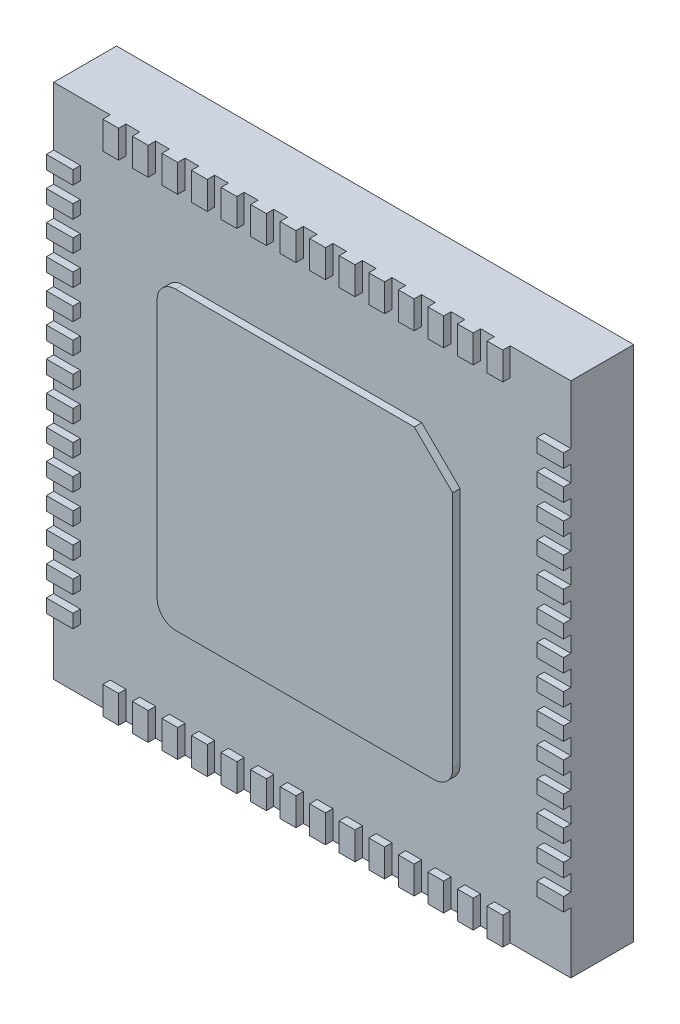
SolidWorks part; units mm, degrees
material "Plastique personnalisé"
ref_plane "Plan de face" through (0, 0, 0) normal (0, 0, 1) x (1, 0, 0)
ref_plane "Plan de dessus" through (0, 0, 0) normal (0, 1, 0) x (1, 0, 0)
ref_plane "Plan de droite" through (0, 0, 0) normal (1, 0, 0) x (0, 0, -1)
sketch "package" plane through (0, 0, 0) normal (0, 0, 1) x (1, 0, 0)
  line L0 (23.2812, 236.9529) -> (30.2812, 236.9529) construction
  line L1 (23.3092, 236.9405) -> (30.3092, 229.9405) construction
  line L2 (23.3092, 236.9405) -> (30.3092, 236.9405)
  line L3 (23.3092, 236.9405) -> (23.3092, 229.9405)
  line L4 (23.3092, 229.9405) -> (30.3092, 229.9405)
  line L5 (30.3092, 236.9405) -> (30.3092, 229.9405)
  dimension "D1" = 7
  dimension "D2" = 7
  dimension "D3" = 7
sketch "Esquisse2" plane through (0, 0, 0) normal (0, 0, 1) x (1, 0, 0)
  line L0 (23.3092, 236.9405) -> (30.3092, 229.9405) construction
  line L1 (25.0592, 231.4405) -> (28.5592, 231.4405)
  line L2 (24.8092, 231.6905) -> (24.8092, 235.1905)
  line L3 (25.0592, 235.4405) -> (28.2902, 235.4405)
  line L4 (28.8092, 231.6905) -> (28.8092, 234.928)
  line L5 (24.8092, 231.4405) -> (28.5514, 235.1826) construction
  line L6 (24.8092, 235.4405) -> (28.8092, 231.4405) construction
  line L7 (28.2902, 235.4405) -> (28.8092, 234.928)
  line L8 (23.3092, 236.9405) -> (30.3092, 236.9405) construction
  line L9 (24.0739, 236.9405) -> (24.2874, 236.9405)
  line L10 (24.0739, 236.9405) -> (24.0739, 236.5655)
  line L11 (24.0739, 236.5655) -> (24.2874, 236.5655)
  line L12 (24.2874, 236.9405) -> (24.2874, 236.5655)
  line L13 (24.4739, 236.9405) -> (24.4739, 236.5655)
  line L14 (24.4739, 236.9405) -> (24.6874, 236.9405)
  line L15 (24.6874, 236.9405) -> (24.6874, 236.5655)
  line L16 (24.4739, 236.5655) -> (24.6874, 236.5655)
  line L17 (24.8739, 236.9405) -> (24.8739, 236.5655)
  line L18 (24.8739, 236.9405) -> (25.0874, 236.9405)
  line L19 (25.0874, 236.9405) -> (25.0874, 236.5655)
  line L20 (24.8739, 236.5655) -> (25.0874, 236.5655)
  line L21 (25.2739, 236.9405) -> (25.2739, 236.5655)
  line L22 (25.2739, 236.9405) -> (25.4874, 236.9405)
  line L23 (25.4874, 236.9405) -> (25.4874, 236.5655)
  line L24 (25.2739, 236.5655) -> (25.4874, 236.5655)
  line L25 (25.6739, 236.9405) -> (25.6739, 236.5655)
  line L26 (25.6739, 236.9405) -> (25.8874, 236.9405)
  line L27 (25.8874, 236.9405) -> (25.8874, 236.5655)
  line L28 (25.6739, 236.5655) -> (25.8874, 236.5655)
  line L29 (26.0739, 236.9405) -> (26.0739, 236.5655)
  line L30 (26.0739, 236.9405) -> (26.2874, 236.9405)
  line L31 (26.2874, 236.9405) -> (26.2874, 236.5655)
  line L32 (26.0739, 236.5655) -> (26.2874, 236.5655)
  line L33 (26.4739, 236.9405) -> (26.4739, 236.5655)
  line L34 (26.4739, 236.9405) -> (26.6874, 236.9405)
  line L35 (26.6874, 236.9405) -> (26.6874, 236.5655)
  line L36 (26.4739, 236.5655) -> (26.6874, 236.5655)
  line L37 (26.8739, 236.9405) -> (26.8739, 236.5655)
  line L38 (26.8739, 236.9405) -> (27.0874, 236.9405)
  line L39 (27.0874, 236.9405) -> (27.0874, 236.5655)
  line L40 (26.8739, 236.5655) -> (27.0874, 236.5655)
  line L41 (27.2739, 236.9405) -> (27.2739, 236.5655)
  line L42 (27.2739, 236.9405) -> (27.4874, 236.9405)
  line L43 (27.4874, 236.9405) -> (27.4874, 236.5655)
  line L44 (27.2739, 236.5655) -> (27.4874, 236.5655)
  line L45 (27.6739, 236.9405) -> (27.6739, 236.5655)
  line L46 (27.6739, 236.9405) -> (27.8874, 236.9405)
  line L47 (27.8874, 236.9405) -> (27.8874, 236.5655)
  line L48 (27.6739, 236.5655) -> (27.8874, 236.5655)
  line L49 (28.0739, 236.9405) -> (28.0739, 236.5655)
  line L50 (28.0739, 236.9405) -> (28.2874, 236.9405)
  line L51 (28.2874, 236.9405) -> (28.2874, 236.5655)
  line L52 (28.0739, 236.5655) -> (28.2874, 236.5655)
  line L53 (28.4739, 236.9405) -> (28.4739, 236.5655)
  line L54 (28.4739, 236.9405) -> (28.6874, 236.9405)
  line L55 (28.6874, 236.9405) -> (28.6874, 236.5655)
  line L56 (28.4739, 236.5655) -> (28.6874, 236.5655)
  line L57 (28.8739, 236.9405) -> (28.8739, 236.5655)
  line L58 (28.8739, 236.9405) -> (29.0874, 236.9405)
  line L59 (29.0874, 236.9405) -> (29.0874, 236.5655)
  line L60 (28.8739, 236.5655) -> (29.0874, 236.5655)
  line L61 (29.2739, 236.9405) -> (29.2739, 236.5655)
  line L62 (29.2739, 236.9405) -> (29.4874, 236.9405)
  line L63 (29.4874, 236.9405) -> (29.4874, 236.5655)
  line L64 (29.2739, 236.5655) -> (29.4874, 236.5655)
  line L65 (23.3092, 233.4405) -> (30.3092, 233.4405) construction
  line L66 (23.3092, 236.9405) -> (23.3092, 229.9405) construction
  line L67 (30.3092, 236.9405) -> (30.3092, 229.9405) construction
  line L68 (23.3092, 235.7459) -> (23.3092, 235.5634)
  line L69 (23.3092, 236.1459) -> (23.6693, 236.1459)
  line L70 (23.3092, 236.1459) -> (23.3092, 235.9634)
  line L71 (23.3092, 235.9634) -> (23.6693, 235.9634)
  line L72 (23.6693, 236.1459) -> (23.6693, 235.9634)
  line L73 (23.3092, 235.7459) -> (23.6693, 235.7459)
  line L74 (23.6693, 235.7459) -> (23.6693, 235.5634)
  line L75 (23.3092, 235.5634) -> (23.6693, 235.5634)
  line L76 (23.3092, 235.3459) -> (23.3092, 235.1634)
  line L77 (23.3092, 235.3459) -> (23.6693, 235.3459)
  line L78 (23.6693, 235.3459) -> (23.6693, 235.1634)
  line L79 (23.3092, 235.1634) -> (23.6693, 235.1634)
  line L80 (23.3092, 234.9459) -> (23.3092, 234.7634)
  line L81 (23.3092, 234.9459) -> (23.6693, 234.9459)
  line L82 (23.6693, 234.9459) -> (23.6693, 234.7634)
  line L83 (23.3092, 234.7634) -> (23.6693, 234.7634)
  line L84 (23.3092, 234.5459) -> (23.3092, 234.3634)
  line L85 (23.3092, 234.5459) -> (23.6693, 234.5459)
  line L86 (23.6693, 234.5459) -> (23.6693, 234.3634)
  line L87 (23.3092, 234.3634) -> (23.6693, 234.3634)
  line L88 (23.3092, 234.1459) -> (23.3092, 233.9634)
  line L89 (23.3092, 234.1459) -> (23.6693, 234.1459)
  line L90 (23.6693, 234.1459) -> (23.6693, 233.9634)
  line L91 (23.3092, 233.9634) -> (23.6693, 233.9634)
  line L92 (23.3092, 233.7459) -> (23.3092, 233.5634)
  line L93 (23.3092, 233.7459) -> (23.6693, 233.7459)
  line L94 (23.6693, 233.7459) -> (23.6693, 233.5634)
  line L95 (23.3092, 233.5634) -> (23.6693, 233.5634)
  line L96 (23.3092, 233.3459) -> (23.3092, 233.1634)
  line L97 (23.3092, 233.3459) -> (23.6693, 233.3459)
  line L98 (23.6693, 233.3459) -> (23.6693, 233.1634)
  line L99 (23.3092, 233.1634) -> (23.6693, 233.1634)
  line L100 (23.3092, 232.9459) -> (23.3092, 232.7634)
  line L101 (23.3092, 232.9459) -> (23.6693, 232.9459)
  line L102 (23.6693, 232.9459) -> (23.6693, 232.7634)
  line L103 (23.3092, 232.7634) -> (23.6693, 232.7634)
  line L104 (23.3092, 232.5459) -> (23.3092, 232.3634)
  line L105 (23.3092, 232.5459) -> (23.6693, 232.5459)
  line L106 (23.6693, 232.5459) -> (23.6693, 232.3634)
  line L107 (23.3092, 232.3634) -> (23.6693, 232.3634)
  line L108 (23.3092, 232.1459) -> (23.3092, 231.9634)
  line L109 (23.3092, 232.1459) -> (23.6693, 232.1459)
  line L110 (23.6693, 232.1459) -> (23.6693, 231.9634)
  line L111 (23.3092, 231.9634) -> (23.6693, 231.9634)
  line L112 (23.3092, 231.7459) -> (23.3092, 231.5634)
  line L113 (23.3092, 231.7459) -> (23.6693, 231.7459)
  line L114 (23.6693, 231.7459) -> (23.6693, 231.5634)
  line L115 (23.3092, 231.5634) -> (23.6693, 231.5634)
  line L116 (23.3092, 231.3459) -> (23.3092, 231.1634)
  line L117 (23.3092, 231.3459) -> (23.6693, 231.3459)
  line L118 (23.6693, 231.3459) -> (23.6693, 231.1634)
  line L119 (23.3092, 231.1634) -> (23.6693, 231.1634)
  line L120 (23.3092, 230.9459) -> (23.3092, 230.7634)
  line L121 (23.3092, 230.9459) -> (23.6693, 230.9459)
  line L122 (23.6693, 230.9459) -> (23.6693, 230.7634)
  line L123 (23.3092, 230.7634) -> (23.6693, 230.7634)
  line L124 (29.2739, 229.9405) -> (29.4874, 229.9405)
  line L125 (29.2739, 229.9405) -> (29.2739, 230.3154)
  line L126 (29.2739, 230.3154) -> (29.4874, 230.3154)
  line L127 (29.4874, 229.9405) -> (29.4874, 230.3154)
  line L128 (28.8739, 229.9405) -> (29.0874, 229.9405)
  line L129 (28.8739, 229.9405) -> (28.8739, 230.3154)
  line L130 (28.8739, 230.3154) -> (29.0874, 230.3154)
  line L131 (29.0874, 229.9405) -> (29.0874, 230.3154)
  line L132 (28.4739, 229.9405) -> (28.6874, 229.9405)
  line L133 (28.4739, 229.9405) -> (28.4739, 230.3154)
  line L134 (28.4739, 230.3154) -> (28.6874, 230.3154)
  line L135 (28.6874, 229.9405) -> (28.6874, 230.3154)
  line L136 (28.0739, 229.9405) -> (28.2874, 229.9405)
  line L137 (28.0739, 229.9405) -> (28.0739, 230.3154)
  line L138 (28.0739, 230.3154) -> (28.2874, 230.3154)
  line L139 (28.2874, 229.9405) -> (28.2874, 230.3154)
  line L140 (27.6739, 229.9405) -> (27.8874, 229.9405)
  line L141 (27.6739, 229.9405) -> (27.6739, 230.3154)
  line L142 (27.6739, 230.3154) -> (27.8874, 230.3154)
  line L143 (27.8874, 229.9405) -> (27.8874, 230.3154)
  line L144 (27.2739, 229.9405) -> (27.4874, 229.9405)
  line L145 (27.2739, 229.9405) -> (27.2739, 230.3154)
  line L146 (27.2739, 230.3154) -> (27.4874, 230.3154)
  line L147 (27.4874, 229.9405) -> (27.4874, 230.3154)
  line L148 (26.8739, 229.9405) -> (27.0874, 229.9405)
  line L149 (26.8739, 229.9405) -> (26.8739, 230.3154)
  line L150 (26.8739, 230.3154) -> (27.0874, 230.3154)
  line L151 (27.0874, 229.9405) -> (27.0874, 230.3154)
  line L152 (26.4739, 229.9405) -> (26.6874, 229.9405)
  line L153 (26.4739, 229.9405) -> (26.4739, 230.3154)
  line L154 (26.4739, 230.3154) -> (26.6874, 230.3154)
  line L155 (26.6874, 229.9405) -> (26.6874, 230.3154)
  line L156 (26.0739, 229.9405) -> (26.2874, 229.9405)
  line L157 (26.0739, 229.9405) -> (26.0739, 230.3154)
  line L158 (26.0739, 230.3154) -> (26.2874, 230.3154)
  line L159 (26.2874, 229.9405) -> (26.2874, 230.3154)
  line L160 (25.6739, 229.9405) -> (25.8874, 229.9405)
  line L161 (25.6739, 229.9405) -> (25.6739, 230.3154)
  line L162 (25.6739, 230.3154) -> (25.8874, 230.3154)
  line L163 (25.8874, 229.9405) -> (25.8874, 230.3154)
  line L164 (25.2739, 229.9405) -> (25.4874, 229.9405)
  line L165 (25.2739, 229.9405) -> (25.2739, 230.3154)
  line L166 (25.2739, 230.3154) -> (25.4874, 230.3154)
  line L167 (25.4874, 229.9405) -> (25.4874, 230.3154)
  line L168 (24.8739, 229.9405) -> (25.0874, 229.9405)
  line L169 (24.8739, 229.9405) -> (24.8739, 230.3154)
  line L170 (24.8739, 230.3154) -> (25.0874, 230.3154)
  line L171 (25.0874, 229.9405) -> (25.0874, 230.3154)
  line L172 (24.4739, 229.9405) -> (24.4739, 230.3154)
  line L173 (24.4739, 229.9405) -> (24.6874, 229.9405)
  line L174 (24.6874, 229.9405) -> (24.6874, 230.3154)
  line L175 (24.4739, 230.3154) -> (24.6874, 230.3154)
  line L176 (24.0739, 229.9405) -> (24.2874, 229.9405)
  line L177 (24.0739, 229.9405) -> (24.0739, 230.3154)
  line L178 (24.0739, 230.3154) -> (24.2874, 230.3154)
  line L179 (24.2874, 229.9405) -> (24.2874, 230.3154)
  line L180 (26.8092, 233.4405) -> (26.8092, 227.4047) construction
  line L181 (30.3092, 230.7634) -> (29.9491, 230.7634)
  line L182 (29.9491, 230.9459) -> (29.9491, 230.7634)
  line L183 (30.3092, 230.9459) -> (29.9491, 230.9459)
  line L184 (30.3092, 230.9459) -> (30.3092, 230.7634)
  line L185 (30.3092, 231.1634) -> (29.9491, 231.1634)
  line L186 (29.9491, 231.3459) -> (29.9491, 231.1634)
  line L187 (30.3092, 231.3459) -> (29.9491, 231.3459)
  line L188 (30.3092, 231.3459) -> (30.3092, 231.1634)
  line L189 (30.3092, 231.5634) -> (29.9491, 231.5634)
  line L190 (29.9491, 231.7459) -> (29.9491, 231.5634)
  line L191 (30.3092, 231.7459) -> (29.9491, 231.7459)
  line L192 (30.3092, 231.7459) -> (30.3092, 231.5634)
  line L193 (30.3092, 231.9634) -> (29.9491, 231.9634)
  line L194 (29.9491, 232.1459) -> (29.9491, 231.9634)
  line L195 (30.3092, 232.1459) -> (29.9491, 232.1459)
  line L196 (30.3092, 232.1459) -> (30.3092, 231.9634)
  line L197 (30.3092, 232.3634) -> (29.9491, 232.3634)
  line L198 (29.9491, 232.5459) -> (29.9491, 232.3634)
  line L199 (30.3092, 232.5459) -> (29.9491, 232.5459)
  line L200 (30.3092, 232.5459) -> (30.3092, 232.3634)
  line L201 (30.3092, 232.7634) -> (29.9491, 232.7634)
  line L202 (29.9491, 232.9459) -> (29.9491, 232.7634)
  line L203 (30.3092, 232.9459) -> (29.9491, 232.9459)
  line L204 (30.3092, 232.9459) -> (30.3092, 232.7634)
  line L205 (30.3092, 233.1634) -> (29.9491, 233.1634)
  line L206 (29.9491, 233.3459) -> (29.9491, 233.1634)
  line L207 (30.3092, 233.3459) -> (29.9491, 233.3459)
  line L208 (30.3092, 233.3459) -> (30.3092, 233.1634)
  line L209 (30.3092, 233.5634) -> (29.9491, 233.5634)
  line L210 (29.9491, 233.7459) -> (29.9491, 233.5634)
  line L211 (30.3092, 233.7459) -> (29.9491, 233.7459)
  line L212 (30.3092, 233.7459) -> (30.3092, 233.5634)
  line L213 (30.3092, 233.9634) -> (29.9491, 233.9634)
  line L214 (29.9491, 234.1459) -> (29.9491, 233.9634)
  line L215 (30.3092, 234.1459) -> (29.9491, 234.1459)
  line L216 (30.3092, 234.1459) -> (30.3092, 233.9634)
  line L217 (30.3092, 234.3634) -> (29.9491, 234.3634)
  line L218 (29.9491, 234.5459) -> (29.9491, 234.3634)
  line L219 (30.3092, 234.5459) -> (29.9491, 234.5459)
  line L220 (30.3092, 234.5459) -> (30.3092, 234.3634)
  line L221 (30.3092, 234.7634) -> (29.9491, 234.7634)
  line L222 (29.9491, 234.9459) -> (29.9491, 234.7634)
  line L223 (30.3092, 234.9459) -> (29.9491, 234.9459)
  line L224 (30.3092, 234.9459) -> (30.3092, 234.7634)
  line L225 (30.3092, 235.1634) -> (29.9491, 235.1634)
  line L226 (29.9491, 235.3459) -> (29.9491, 235.1634)
  line L227 (30.3092, 235.3459) -> (29.9491, 235.3459)
  line L228 (30.3092, 235.3459) -> (30.3092, 235.1634)
  line L229 (30.3092, 235.5634) -> (29.9491, 235.5634)
  line L230 (29.9491, 235.7459) -> (29.9491, 235.5634)
  line L231 (30.3092, 235.7459) -> (29.9491, 235.7459)
  line L232 (29.9491, 236.1459) -> (29.9491, 235.9634)
  line L233 (30.3092, 235.9634) -> (29.9491, 235.9634)
  line L234 (30.3092, 236.1459) -> (30.3092, 235.9634)
  line L235 (30.3092, 236.1459) -> (29.9491, 236.1459)
  line L236 (30.3092, 235.7459) -> (30.3092, 235.5634)
  arc A0 (28.5592, 231.4405) -> (28.8092, 231.6905) centre (28.5592, 231.6905) ccw
  arc A1 (25.0592, 231.4405) -> (24.8092, 231.6905) centre (25.0592, 231.6905) cw
  arc A2 (24.8092, 235.1905) -> (25.0592, 235.4405) centre (25.0592, 235.1905) cw
  point P0 (26.8092, 233.4405)
  dimension "D1" = 0.25
  dimension "D2" = 4
  dimension "D3" = 14
  dimension "D4" = 14
extrude "Boss.-Extru.1" add sketch "package" against normal blind 0.85
extrude "Boss.-Extru.2" add sketch "Esquisse2" along normal blind 0.1
sketch "Esquisse3" plane through (0, 0, -0.85) normal (0, 0, -1) x (-1, 0, 0)
  circle A0 centre (-29.9746, 236.5813) radius 0.1661
extrude "Enlèv. mat.-Extru.1" cut sketch "Esquisse3" against normal blind 0.1
sketch "Esquisse4" plane through (-0.3704, 1.1024, -0.85) normal (0, 0, -1) x (-1, 0, 0)
  line L8 (-28.6829, 230.452) -> (-28.6867, 230.4847)
  line L9 (-28.6867, 230.4847) -> (-28.8383, 230.4808)
  line L10 (-28.8383, 230.4808) -> (-28.99, 230.4769)
  line L11 (-28.99, 230.4769) -> (-28.99, 230.5964)
  line L12 (-28.99, 230.5964) -> (-28.99, 230.7159)
  line L13 (-28.99, 230.7159) -> (-28.8562, 230.7193)
  line L14 (-28.8562, 230.7193) -> (-28.7223, 230.7226)
  line L15 (-28.7223, 230.7226) -> (-28.7223, 230.7524)
  line L16 (-28.7223, 230.7524) -> (-28.7223, 230.7821)
  line L17 (-28.7223, 230.7821) -> (-28.8562, 230.7855)
  line L18 (-28.8562, 230.7855) -> (-28.99, 230.7888)
  line L19 (-28.99, 230.7888) -> (-28.99, 230.9015)
  line L20 (-28.99, 230.9015) -> (-28.99, 231.0141)
  line L21 (-28.99, 231.0141) -> (-28.8413, 231.0141)
  line L22 (-28.8413, 231.0141) -> (-28.6926, 231.0141)
  line L23 (-28.6926, 231.0141) -> (-28.6926, 231.0438)
  line L24 (-28.6926, 231.0438) -> (-28.6926, 231.0736)
  line L25 (-28.6926, 231.0736) -> (-28.877, 231.0736)
  line L26 (-28.877, 231.0736) -> (-29.0614, 231.0736)
  line L27 (-29.0614, 231.0736) -> (-29.0614, 230.7464)
  line L28 (-29.0614, 230.7464) -> (-29.0614, 230.4193)
  line L29 (-29.0614, 230.4193) -> (-28.8703, 230.4193)
  line L30 (-28.8703, 230.4193) -> (-28.6791, 230.4193)
  line L31 (-28.6791, 230.4193) -> (-28.6829, 230.452)
  line L32 (-28.0383, 230.5561) -> (-28.0383, 230.6929)
  line L33 (-28.0383, 230.6929) -> (-27.936, 230.6929)
  line L34 (-27.9661, 231.0708) -> (-28.102, 231.0676)
  line L35 (-28.102, 231.0676) -> (-28.0999, 230.7464)
  line L36 (-28.0681, 230.4193) -> (-28.0383, 230.4193)
  line L37 (-28.0383, 230.4193) -> (-28.0383, 230.5561)
  line L38 (-28.0383, 230.8832) -> (-28.0383, 231.0141)
  line L39 (-28.0383, 231.0141) -> (-27.9485, 231.0141)
  line L40 (-27.9485, 230.7524) -> (-28.0383, 230.7524)
  line L41 (-28.0383, 230.7524) -> (-28.0383, 230.8832)
  line L42 (-26.8488, 230.4526) -> (-26.8488, 230.4858)
  line L43 (-26.8488, 230.4858) -> (-26.9614, 230.4809)
  line L44 (-27.0213, 230.4193) -> (-26.8488, 230.4193)
  line L45 (-26.8488, 230.4193) -> (-26.8488, 230.4526)
  line L46 (-26.3989, 230.7459) -> (-26.3951, 230.7762)
  line L47 (-26.3951, 230.7762) -> (-26.5803, 230.7762)
  line L48 (-26.5803, 230.7762) -> (-26.7655, 230.7762)
  line L49 (-26.7655, 230.7762) -> (-26.7655, 230.7484)
  line L50 (-26.5791, 230.7132) -> (-26.4027, 230.7156)
  line L51 (-26.4027, 230.7156) -> (-26.3989, 230.7459)
  line L52 (-26.2439, 232.1836) -> (-26.2161, 232.2135)
  line L53 (-26.2161, 232.2135) -> (-26.2512, 232.2502)
  line L54 (-28.1351, 234.1342) -> (-28.1724, 234.1715)
  line L55 (-28.1724, 234.1715) -> (-28.2316, 234.1066)
  line L56 (-26.9889, 232.0679) -> (-26.8971, 232.0359)
  line L57 (-26.8971, 232.0359) -> (-26.8013, 232.069)
  line L58 (-26.2003, 232.5814) -> (-26.1572, 232.6439)
  line L59 (-26.1572, 232.6439) -> (-26.1821, 232.7689)
  line L60 (-27.6008, 234.2028) -> (-27.7112, 234.2254)
  line L61 (-27.7112, 234.2254) -> (-27.804, 234.1694)
  line L62 (-27.9383, 234.0792) -> (-27.9798, 234.045)
  line L63 (-27.9798, 234.045) -> (-27.9764, 233.9541)
  line L64 (-27.9764, 233.9541) -> (-27.9729, 233.8631)
  line L65 (-27.9729, 233.8631) -> (-27.9313, 233.8602)
  line L66 (-26.5276, 232.4654) -> (-26.5276, 232.4059)
  line L67 (-26.5276, 232.4059) -> (-26.4235, 232.4061)
  line L68 (-26.4235, 232.4061) -> (-26.3194, 232.4063)
  line L69 (-26.3194, 232.4063) -> (-26.2814, 232.4626)
  line L70 (-27.1822, 234.3566) -> (-27.2956, 234.3568)
  line L71 (-27.2956, 234.3568) -> (-27.3097, 234.3194)
  spline S0 degree 3 poles (-28.3034, 230.4273) (-28.2435, 230.4557) (-28.2169, 230.5058) (-28.2168, 230.5902) knots 0 0 0 0 1 1 1 1
  spline S1 degree 3 poles (-28.2168, 230.5902) (-28.2168, 230.6551) (-28.2199, 230.6631) (-28.2614, 230.7044) knots 0 0 0 0 1 1 1 1
  spline S2 degree 3 poles (-28.2614, 230.7044) (-28.2883, 230.7311) (-28.3343, 230.7589) (-28.3774, 230.7744) knots 0 0 0 0 1 1 1 1
  spline S3 degree 3 poles (-28.3774, 230.7744) (-28.4701, 230.8078) (-28.5031, 230.8271) (-28.531, 230.864) knots 0 0 0 0 1 1 1 1
  spline S4 degree 3 poles (-28.531, 230.864) (-28.5509, 230.8904) (-28.5521, 230.9002) (-28.5401, 230.9402) knots 0 0 0 0 1 1 1 1
  spline S5 degree 3 poles (-28.5401, 230.9402) (-28.5132, 231.03) (-28.3832, 231.0483) (-28.312, 230.9725) knots 0 0 0 0 1 1 1 1
  spline S6 degree 3 poles (-28.312, 230.9725) (-28.2821, 230.9407) (-28.2681, 230.9369) (-28.2419, 230.9536) knots 0 0 0 0 1 1 1 1
  spline S7 degree 3 poles (-28.2419, 230.9536) (-28.2165, 230.9696) (-28.269, 231.0357) (-28.3286, 231.0628) knots 0 0 0 0 1 1 1 1
  spline S8 degree 3 poles (-28.3286, 231.0628) (-28.4159, 231.1024) (-28.5158, 231.084) (-28.5742, 231.0176) knots 0 0 0 0 1 1 1 1
  spline S9 degree 3 poles (-28.5742, 231.0176) (-28.6039, 230.9838) (-28.6093, 230.9675) (-28.6093, 230.913) knots 0 0 0 0 1 1 1 1
  spline S10 degree 3 poles (-28.6093, 230.913) (-28.6093, 230.8584) (-28.6039, 230.8422) (-28.5742, 230.8084) knots 0 0 0 0 1 1 1 1
  spline S11 degree 3 poles (-28.5742, 230.8084) (-28.5549, 230.7864) (-28.5161, 230.7586) (-28.488, 230.7467) knots 0 0 0 0 1 1 1 1
  spline S12 degree 3 poles (-28.488, 230.7467) (-28.3184, 230.6746) (-28.3112, 230.6703) (-28.2948, 230.6309) knots 0 0 0 0 1 1 1 1
  spline S13 degree 3 poles (-28.2948, 230.6309) (-28.2726, 230.5779) (-28.2837, 230.5322) (-28.3277, 230.4952) knots 0 0 0 0 1 1 1 1
  spline S14 degree 3 poles (-28.3277, 230.4952) (-28.3598, 230.4682) (-28.3724, 230.465) (-28.4293, 230.4697) knots 0 0 0 0 1 1 1 1
  spline S15 degree 3 poles (-28.4293, 230.4697) (-28.486, 230.4744) (-28.4995, 230.4808) (-28.5353, 230.5199) knots 0 0 0 0 1 1 1 1
  spline S16 degree 3 poles (-28.5353, 230.5199) (-28.5717, 230.5596) (-28.5795, 230.5632) (-28.6047, 230.5517) knots 0 0 0 0 1 1 1 1
  spline S17 degree 3 poles (-28.6047, 230.5517) (-28.6385, 230.5363) (-28.6393, 230.5287) (-28.6107, 230.4944) knots 0 0 0 0 1 1 1 1
  spline S18 degree 3 poles (-28.6107, 230.4944) (-28.56, 230.4337) (-28.5029, 230.4074) (-28.4221, 230.4074) knots 0 0 0 0 1 1 1 1
  spline S19 degree 3 poles (-28.4221, 230.4074) (-28.375, 230.4074) (-28.3291, 230.4151) (-28.3034, 230.4273) knots 0 0 0 0 1 1 1 1
  spline S20 degree 3 poles (-27.3472, 230.4344) (-27.287, 230.4746) (-27.2629, 230.5298) (-27.2683, 230.6148) knots 0 0 0 0 1 1 1 1
  spline S21 degree 3 poles (-27.2683, 230.6148) (-27.2726, 230.6803) (-27.2765, 230.6885) (-27.3226, 230.7295) knots 0 0 0 0 1 1 1 1
  spline S22 degree 3 poles (-27.3226, 230.7295) (-27.3599, 230.7626) (-27.3679, 230.7753) (-27.3545, 230.7804) knots 0 0 0 0 1 1 1 1
  spline S23 degree 3 poles (-27.3545, 230.7804) (-27.3245, 230.7919) (-27.289, 230.8628) (-27.2889, 230.9112) knots 0 0 0 0 1 1 1 1
  spline S24 degree 3 poles (-27.2889, 230.9112) (-27.2889, 230.9787) (-27.3205, 231.0353) (-27.3733, 231.0623) knots 0 0 0 0 1 1 1 1
  spline S25 degree 3 poles (-27.3733, 231.0623) (-27.4562, 231.1045) (-27.5337, 231.0859) (-27.5916, 231.01) knots 0 0 0 0 1 1 1 1
  spline S26 degree 3 poles (-27.5916, 231.01) (-27.6281, 230.9622) (-27.6294, 230.9475) (-27.5986, 230.931) knots 0 0 0 0 1 1 1 1
  spline S27 degree 3 poles (-27.5986, 230.931) (-27.5787, 230.9204) (-27.5724, 230.924) (-27.5562, 230.9553) knots 0 0 0 0 1 1 1 1
  spline S28 degree 3 poles (-27.5562, 230.9553) (-27.5016, 231.0608) (-27.3603, 231.0245) (-27.3603, 230.9049) knots 0 0 0 0 1 1 1 1
  spline S29 degree 3 poles (-27.3603, 230.9049) (-27.3603, 230.8453) (-27.3999, 230.8034) (-27.4665, 230.7928) knots 0 0 0 0 1 1 1 1
  spline S30 degree 3 poles (-27.4665, 230.7928) (-27.5073, 230.7862) (-27.5149, 230.7806) (-27.5149, 230.7568) knots 0 0 0 0 1 1 1 1
  spline S31 degree 3 poles (-27.5149, 230.7568) (-27.5149, 230.7324) (-27.5092, 230.7286) (-27.4725, 230.7286) knots 0 0 0 0 1 1 1 1
  spline S32 degree 3 poles (-27.4725, 230.7286) (-27.3876, 230.7286) (-27.3371, 230.6799) (-27.3368, 230.5977) knots 0 0 0 0 1 1 1 1
  spline S33 degree 3 poles (-27.3368, 230.5977) (-27.3365, 230.5246) (-27.3729, 230.4796) (-27.4394, 230.4707) knots 0 0 0 0 1 1 1 1
  spline S34 degree 3 poles (-27.4394, 230.4707) (-27.4943, 230.4633) (-27.5574, 230.4916) (-27.5693, 230.5289) knots 0 0 0 0 1 1 1 1
  spline S35 degree 3 poles (-27.5693, 230.5289) (-27.5763, 230.551) (-27.6054, 230.5565) (-27.6305, 230.5406) knots 0 0 0 0 1 1 1 1
  spline S36 degree 3 poles (-27.6305, 230.5406) (-27.6514, 230.5273) (-27.6085, 230.4609) (-27.5596, 230.4311) knots 0 0 0 0 1 1 1 1
  spline S37 degree 3 poles (-27.5596, 230.4311) (-27.5038, 230.3971) (-27.4006, 230.3987) (-27.3472, 230.4344) knots 0 0 0 0 1 1 1 1
  spline S38 degree 3 poles (-26.004, 230.4291) (-25.9575, 230.4534) (-25.909, 230.535) (-25.909, 230.5888) knots 0 0 0 0 1 1 1 1
  spline S39 degree 3 poles (-25.909, 230.5888) (-25.909, 230.6761) (-25.9685, 230.7335) (-26.1164, 230.7888) knots 0 0 0 0 1 1 1 1
  spline S40 degree 3 poles (-26.1164, 230.7888) (-26.2093, 230.8236) (-26.2421, 230.8568) (-26.2421, 230.9165) knots 0 0 0 0 1 1 1 1
  spline S41 degree 3 poles (-26.2421, 230.9165) (-26.2421, 231.0215) (-26.102, 231.0588) (-26.0176, 230.9763) knots 0 0 0 0 1 1 1 1
  spline S42 degree 3 poles (-26.0176, 230.9763) (-25.9915, 230.9508) (-25.9745, 230.943) (-25.957, 230.9485) knots 0 0 0 0 1 1 1 1
  spline S43 degree 3 poles (-25.957, 230.9485) (-25.9255, 230.9585) (-25.9264, 230.969) (-25.9629, 231.0123) knots 0 0 0 0 1 1 1 1
  spline S44 degree 3 poles (-25.9629, 231.0123) (-26.0454, 231.1104) (-26.2174, 231.1051) (-26.2873, 231.0022) knots 0 0 0 0 1 1 1 1
  spline S45 degree 3 poles (-26.2873, 231.0022) (-26.3106, 230.9679) (-26.3147, 230.9494) (-26.3105, 230.8978) knots 0 0 0 0 1 1 1 1
  spline S46 degree 3 poles (-26.3105, 230.8978) (-26.3038, 230.8139) (-26.2669, 230.7766) (-26.1424, 230.7279) knots 0 0 0 0 1 1 1 1
  spline S47 degree 3 poles (-26.1424, 230.7279) (-26.037, 230.6866) (-25.9804, 230.6387) (-25.9804, 230.591) knots 0 0 0 0 1 1 1 1
  spline S48 degree 3 poles (-25.9804, 230.591) (-25.9804, 230.46) (-26.1641, 230.4208) (-26.2524, 230.533) knots 0 0 0 0 1 1 1 1
  spline S49 degree 3 poles (-26.2524, 230.533) (-26.2701, 230.5555) (-26.2834, 230.5619) (-26.301, 230.5563) knots 0 0 0 0 1 1 1 1
  spline S50 degree 3 poles (-26.301, 230.5563) (-26.3144, 230.552) (-26.3253, 230.5413) (-26.3253, 230.5324) knots 0 0 0 0 1 1 1 1
  spline S51 degree 3 poles (-26.3253, 230.5324) (-26.3253, 230.5069) (-26.2646, 230.4415) (-26.2248, 230.4241) knots 0 0 0 0 1 1 1 1
  spline S52 degree 3 poles (-26.2248, 230.4241) (-26.1707, 230.4006) (-26.0534, 230.4032) (-26.004, 230.4291) knots 0 0 0 0 1 1 1 1
  spline S53 degree 3 poles (-25.5456, 230.4434) (-25.4986, 230.4873) (-25.4807, 230.5302) (-25.4807, 230.5987) knots 0 0 0 0 1 1 1 1
  spline S54 degree 3 poles (-25.4807, 230.5987) (-25.4807, 230.6655) (-25.5117, 230.7308) (-25.5543, 230.7535) knots 0 0 0 0 1 1 1 1
  spline S55 degree 3 poles (-25.5543, 230.7535) (-25.578, 230.7662) (-25.578, 230.7664) (-25.5547, 230.792) knots 0 0 0 0 1 1 1 1
  spline S56 degree 3 poles (-25.5547, 230.792) (-25.5174, 230.8331) (-25.5045, 230.8661) (-25.5046, 230.9211) knots 0 0 0 0 1 1 1 1
  spline S57 degree 3 poles (-25.5046, 230.9211) (-25.5047, 231.0911) (-25.7244, 231.146) (-25.8143, 230.9986) knots 0 0 0 0 1 1 1 1
  spline S58 degree 3 poles (-25.8143, 230.9986) (-25.8433, 230.9511) (-25.8432, 230.9465) (-25.8136, 230.9307) knots 0 0 0 0 1 1 1 1
  spline S59 degree 3 poles (-25.8136, 230.9307) (-25.793, 230.9197) (-25.7867, 230.9229) (-25.7694, 230.953) knots 0 0 0 0 1 1 1 1
  spline S60 degree 3 poles (-25.7694, 230.953) (-25.7281, 231.025) (-25.6602, 231.0386) (-25.6027, 230.9866) knots 0 0 0 0 1 1 1 1
  spline S61 degree 3 poles (-25.6027, 230.9866) (-25.5822, 230.9681) (-25.5759, 230.9493) (-25.5759, 230.907) knots 0 0 0 0 1 1 1 1
  spline S62 degree 3 poles (-25.5759, 230.907) (-25.5759, 230.8367) (-25.6126, 230.7972) (-25.6796, 230.7953) knots 0 0 0 0 1 1 1 1
  spline S63 degree 3 poles (-25.6796, 230.7953) (-25.7195, 230.7941) (-25.725, 230.7903) (-25.7284, 230.7613) knots 0 0 0 0 1 1 1 1
  spline S64 degree 3 poles (-25.7284, 230.7613) (-25.732, 230.7299) (-25.73, 230.7286) (-25.6791, 230.7286) knots 0 0 0 0 1 1 1 1
  spline S65 degree 3 poles (-25.6791, 230.7286) (-25.6369, 230.7286) (-25.6184, 230.7215) (-25.5891, 230.6941) knots 0 0 0 0 1 1 1 1
  spline S66 degree 3 poles (-25.5891, 230.6941) (-25.5569, 230.6641) (-25.5521, 230.6515) (-25.5521, 230.598) knots 0 0 0 0 1 1 1 1
  spline S67 degree 3 poles (-25.5521, 230.598) (-25.5521, 230.5458) (-25.5574, 230.5311) (-25.5869, 230.5016) knots 0 0 0 0 1 1 1 1
  spline S68 degree 3 poles (-25.5869, 230.5016) (-25.6388, 230.4498) (-25.7066, 230.4524) (-25.7627, 230.5085) knots 0 0 0 0 1 1 1 1
  spline S69 degree 3 poles (-25.7627, 230.5085) (-25.8075, 230.5533) (-25.8115, 230.555) (-25.8358, 230.5396) knots 0 0 0 0 1 1 1 1
  spline S70 degree 3 poles (-25.8358, 230.5396) (-25.8591, 230.5249) (-25.8232, 230.4605) (-25.7746, 230.43) knots 0 0 0 0 1 1 1 1
  spline S71 degree 3 poles (-25.7746, 230.43) (-25.7183, 230.3947) (-25.5898, 230.4022) (-25.5456, 230.4434) knots 0 0 0 0 1 1 1 1
  spline S72 degree 3 poles (-27.936, 230.6929) (-27.7657, 230.6929) (-27.6993, 230.7446) (-27.6994, 230.8773) knots 0 0 0 0 1 1 1 1
  spline S73 degree 3 poles (-27.6994, 230.8773) (-27.6995, 230.9634) (-27.7279, 231.019) (-27.7885, 231.0516) knots 0 0 0 0 1 1 1 1
  spline S74 degree 3 poles (-27.7885, 231.0516) (-27.8236, 231.0705) (-27.8516, 231.0735) (-27.9661, 231.0708) knots 0 0 0 0 1 1 1 1
  spline S75 degree 3 poles (-28.0999, 230.7464) (-28.0988, 230.5698) (-28.0979, 230.4239) (-28.0979, 230.4223) knots 0 0 0 0 1 1 1 1
  spline S76 degree 3 poles (-28.0979, 230.4223) (-28.0979, 230.4206) (-28.0844, 230.4193) (-28.0681, 230.4193) knots 0 0 0 0 1 1 1 1
  spline S77 degree 3 poles (-27.9485, 231.0141) (-27.8166, 231.0141) (-27.7647, 230.9771) (-27.7647, 230.8832) knots 0 0 0 0 1 1 1 1
  spline S78 degree 3 poles (-27.7647, 230.8832) (-27.7647, 230.7893) (-27.8166, 230.7524) (-27.9485, 230.7524) knots 0 0 0 0 1 1 1 1
  spline S79 degree 3 poles (-26.9614, 230.4809) (-27.1059, 230.4746) (-27.1174, 230.4785) (-27.0929, 230.5257) knots 0 0 0 0 1 1 1 1
  spline S80 degree 3 poles (-27.0929, 230.5257) (-27.0828, 230.5453) (-27.0348, 230.6037) (-26.9863, 230.6557) knots 0 0 0 0 1 1 1 1
  spline S81 degree 3 poles (-26.9863, 230.6557) (-26.9377, 230.7076) (-26.8869, 230.7718) (-26.8734, 230.7983) knots 0 0 0 0 1 1 1 1
  spline S82 degree 3 poles (-26.8734, 230.7983) (-26.84, 230.8638) (-26.8404, 230.9561) (-26.8744, 231.0111) knots 0 0 0 0 1 1 1 1
  spline S83 degree 3 poles (-26.8744, 231.0111) (-26.9347, 231.1087) (-27.0961, 231.1095) (-27.1549, 231.0125) knots 0 0 0 0 1 1 1 1
  spline S84 degree 3 poles (-27.1549, 231.0125) (-27.1944, 230.9472) (-27.1982, 230.9221) (-27.1709, 230.9075) knots 0 0 0 0 1 1 1 1
  spline S85 degree 3 poles (-27.1709, 230.9075) (-27.1498, 230.8962) (-27.144, 230.9003) (-27.1227, 230.9421) knots 0 0 0 0 1 1 1 1
  spline S86 degree 3 poles (-27.1227, 230.9421) (-27.0951, 230.9962) (-27.0684, 231.0141) (-27.0153, 231.0141) knots 0 0 0 0 1 1 1 1
  spline S87 degree 3 poles (-27.0153, 231.0141) (-26.962, 231.0141) (-26.9359, 230.9963) (-26.9204, 230.9495) knots 0 0 0 0 1 1 1 1
  spline S88 degree 3 poles (-26.9204, 230.9495) (-26.8969, 230.878) (-26.9211, 230.8246) (-27.0354, 230.696) knots 0 0 0 0 1 1 1 1
  spline S89 degree 3 poles (-27.0354, 230.696) (-27.1314, 230.588) (-27.1934, 230.4877) (-27.1936, 230.4401) knots 0 0 0 0 1 1 1 1
  spline S90 degree 3 poles (-27.1936, 230.4401) (-27.1937, 230.4212) (-27.1777, 230.4193) (-27.0213, 230.4193) knots 0 0 0 0 1 1 1 1
  spline S91 degree 3 poles (-26.7655, 230.7484) (-26.7655, 230.7331) (-26.7633, 230.7184) (-26.7605, 230.7157) knots 0 0 0 0 1 1 1 1
  spline S92 degree 3 poles (-26.7605, 230.7157) (-26.7578, 230.713) (-26.6762, 230.7118) (-26.5791, 230.7132) knots 0 0 0 0 1 1 1 1
  spline S93 degree 3 poles (-26.9045, 231.8347) (-26.7387, 231.8711) (-26.6049, 231.9252) (-26.4562, 232.016) knots 0 0 0 0 1 1 1 1
  spline S94 degree 3 poles (-26.4562, 232.016) (-26.401, 232.0497) (-26.2789, 232.1462) (-26.2439, 232.1836) knots 0 0 0 0 1 1 1 1
  spline S95 degree 3 poles (-26.2512, 232.2502) (-26.2705, 232.2704) (-26.2894, 232.2869) (-26.2933, 232.2869) knots 0 0 0 0 1 1 1 1
  spline S96 degree 3 poles (-26.2933, 232.2869) (-26.2972, 232.2869) (-26.3153, 232.2729) (-26.3336, 232.2557) knots 0 0 0 0 1 1 1 1
  spline S97 degree 3 poles (-26.3336, 232.2557) (-26.4695, 232.1282) (-26.6821, 232.0114) (-26.8725, 231.9595) knots 0 0 0 0 1 1 1 1
  spline S98 degree 3 poles (-26.8725, 231.9595) (-27.0127, 231.9213) (-27.2272, 231.9083) (-27.3732, 231.9291) knots 0 0 0 0 1 1 1 1
  spline S99 degree 3 poles (-27.3732, 231.9291) (-27.6004, 231.9616) (-27.8595, 232.0795) (-28.0264, 232.2264) knots 0 0 0 0 1 1 1 1
  spline S100 degree 3 poles (-28.0264, 232.2264) (-28.0676, 232.2625) (-28.0676, 232.2628) (-28.0324, 232.2453) knots 0 0 0 0 1 1 1 1
  spline S101 degree 3 poles (-28.0324, 232.2453) (-27.9349, 232.1969) (-27.8023, 232.2498) (-27.7573, 232.355) knots 0 0 0 0 1 1 1 1
  spline S102 degree 3 poles (-27.7573, 232.355) (-27.736, 232.4047) (-27.7364, 232.4816) (-27.7582, 232.5237) knots 0 0 0 0 1 1 1 1
  spline S103 degree 3 poles (-27.7582, 232.5237) (-27.7827, 232.571) (-27.8516, 232.6282) (-27.8958, 232.6379) knots 0 0 0 0 1 1 1 1
  spline S104 degree 3 poles (-27.8958, 232.6379) (-28.0633, 232.6747) (-28.1968, 232.5184) (-28.1398, 232.3524) knots 0 0 0 0 1 1 1 1
  spline S105 degree 3 poles (-28.1398, 232.3524) (-28.1213, 232.2987) (-28.2531, 232.4739) (-28.3141, 232.5843) knots 0 0 0 0 1 1 1 1
  spline S106 degree 3 poles (-28.3141, 232.5843) (-28.359, 232.6655) (-28.4172, 232.8241) (-28.4375, 232.9205) knots 0 0 0 0 1 1 1 1
  spline S107 degree 3 poles (-28.4375, 232.9205) (-28.5198, 233.311) (-28.4105, 233.7332) (-28.1529, 234.0195) knots 0 0 0 0 1 1 1 1
  spline S108 degree 3 poles (-28.1529, 234.0195) (-28.1226, 234.0532) (-28.0978, 234.0844) (-28.0978, 234.0888) knots 0 0 0 0 1 1 1 1
  spline S109 degree 3 poles (-28.0978, 234.0888) (-28.0978, 234.0933) (-28.1146, 234.1137) (-28.1351, 234.1342) knots 0 0 0 0 1 1 1 1
  spline S110 degree 3 poles (-28.2316, 234.1066) (-28.3948, 233.9273) (-28.5166, 233.6733) (-28.5624, 233.417) knots 0 0 0 0 1 1 1 1
  spline S111 degree 3 poles (-28.5624, 233.417) (-28.5821, 233.3067) (-28.5788, 233.0369) (-28.5564, 232.9293) knots 0 0 0 0 1 1 1 1
  spline S112 degree 3 poles (-28.5564, 232.9293) (-28.4307, 232.3263) (-27.9742, 231.8965) (-27.3686, 231.811) knots 0 0 0 0 1 1 1 1
  spline S113 degree 3 poles (-27.3686, 231.811) (-27.2542, 231.7949) (-27.0354, 231.806) (-26.9045, 231.8347) knots 0 0 0 0 1 1 1 1
  spline S114 degree 3 poles (-27.2678, 232.0698) (-27.2032, 232.1917) (-27.1765, 232.3012) (-27.1771, 232.4416) knots 0 0 0 0 1 1 1 1
  spline S115 degree 3 poles (-27.1771, 232.4416) (-27.1776, 232.5787) (-27.1968, 232.663) (-27.2529, 232.7741) knots 0 0 0 0 1 1 1 1
  spline S116 degree 3 poles (-27.2529, 232.7741) (-27.3794, 233.0247) (-27.5982, 233.1722) (-27.8988, 233.2093) knots 0 0 0 0 1 1 1 1
  spline S117 degree 3 poles (-27.8988, 233.2093) (-27.9901, 233.2206) (-28.0201, 233.2958) (-27.9485, 233.3341) knots 0 0 0 0 1 1 1 1
  spline S118 degree 3 poles (-27.9485, 233.3341) (-27.9236, 233.3474) (-27.9029, 233.3476) (-27.8267, 233.3348) knots 0 0 0 0 1 1 1 1
  spline S119 degree 3 poles (-27.8267, 233.3348) (-27.5105, 233.2821) (-27.2703, 233.109) (-27.14, 232.8401) knots 0 0 0 0 1 1 1 1
  spline S120 degree 3 poles (-27.14, 232.8401) (-27.0599, 232.6747) (-27.0452, 232.6072) (-27.0461, 232.4059) knots 0 0 0 0 1 1 1 1
  spline S121 degree 3 poles (-27.0461, 232.4059) (-27.0467, 232.2544) (-27.05, 232.2263) (-27.0731, 232.1749) knots 0 0 0 0 1 1 1 1
  spline S122 degree 3 poles (-27.0731, 232.1749) (-27.0876, 232.1428) (-27.0952, 232.1127) (-27.0901, 232.1082) knots 0 0 0 0 1 1 1 1
  spline S123 degree 3 poles (-27.0901, 232.1082) (-27.0849, 232.1036) (-27.0394, 232.0855) (-26.9889, 232.0679) knots 0 0 0 0 1 1 1 1
  spline S124 degree 3 poles (-26.8013, 232.069) (-26.7115, 232.1001) (-26.7047, 232.1048) (-26.6943, 232.144) knots 0 0 0 0 1 1 1 1
  spline S125 degree 3 poles (-26.6943, 232.144) (-26.6159, 232.4379) (-26.6774, 232.8278) (-26.8443, 233.0957) knots 0 0 0 0 1 1 1 1
  spline S126 degree 3 poles (-26.8443, 233.0957) (-27.0629, 233.4468) (-27.3616, 233.6458) (-27.7657, 233.7098) knots 0 0 0 0 1 1 1 1
  spline S127 degree 3 poles (-27.7657, 233.7098) (-27.9173, 233.7338) (-28.0097, 233.7251) (-28.1114, 233.6772) knots 0 0 0 0 1 1 1 1
  spline S128 degree 3 poles (-28.1114, 233.6772) (-28.2851, 233.5953) (-28.3666, 233.4529) (-28.3577, 233.2464) knots 0 0 0 0 1 1 1 1
  spline S129 degree 3 poles (-28.3577, 233.2464) (-28.3527, 233.1286) (-28.3164, 233.0452) (-28.2345, 232.9633) knots 0 0 0 0 1 1 1 1
  spline S130 degree 3 poles (-28.2345, 232.9633) (-28.1582, 232.887) (-28.0747, 232.8478) (-27.9603, 232.8346) knots 0 0 0 0 1 1 1 1
  spline S131 degree 3 poles (-27.9603, 232.8346) (-27.8125, 232.8175) (-27.7404, 232.7849) (-27.6498, 232.6943) knots 0 0 0 0 1 1 1 1
  spline S132 degree 3 poles (-27.6498, 232.6943) (-27.5548, 232.5993) (-27.5261, 232.4019) (-27.589, 232.275) knots 0 0 0 0 1 1 1 1
  spline S133 degree 3 poles (-27.589, 232.275) (-27.6068, 232.2391) (-27.6282, 232.2001) (-27.6365, 232.1885) knots 0 0 0 0 1 1 1 1
  spline S134 degree 3 poles (-27.6365, 232.1885) (-27.6499, 232.1698) (-27.6434, 232.1599) (-27.5816, 232.1052) knots 0 0 0 0 1 1 1 1
  spline S135 degree 3 poles (-27.5816, 232.1052) (-27.5198, 232.0505) (-27.5007, 232.0408) (-27.421, 232.0236) knots 0 0 0 0 1 1 1 1
  spline S136 degree 3 poles (-27.421, 232.0236) (-27.3712, 232.0128) (-27.3246, 232.0035) (-27.3173, 232.0027) knots 0 0 0 0 1 1 1 1
  spline S137 degree 3 poles (-27.3173, 232.0027) (-27.3101, 232.002) (-27.2878, 232.0322) (-27.2678, 232.0698) knots 0 0 0 0 1 1 1 1
  spline S138 degree 3 poles (-26.2814, 232.4626) (-26.2605, 232.4936) (-26.224, 232.547) (-26.2003, 232.5814) knots 0 0 0 0 1 1 1 1
  spline S139 degree 3 poles (-26.1821, 232.7689) (-26.2563, 233.1421) (-26.4169, 233.4516) (-26.6635, 233.6967) knots 0 0 0 0 1 1 1 1
  spline S140 degree 3 poles (-26.6635, 233.6967) (-26.9256, 233.9571) (-27.2453, 234.1297) (-27.6008, 234.2028) knots 0 0 0 0 1 1 1 1
  spline S141 degree 3 poles (-27.804, 234.1694) (-27.855, 234.1386) (-27.9155, 234.098) (-27.9383, 234.0792) knots 0 0 0 0 1 1 1 1
  spline S142 degree 3 poles (-27.9313, 233.8602) (-27.6894, 233.8432) (-27.5245, 233.8027) (-27.3395, 233.7145) knots 0 0 0 0 1 1 1 1
  spline S143 degree 3 poles (-27.3395, 233.7145) (-26.9039, 233.507) (-26.617, 233.1211) (-26.5458, 232.6469) knots 0 0 0 0 1 1 1 1
  spline S144 degree 3 poles (-26.5458, 232.6469) (-26.5358, 232.5798) (-26.5276, 232.4982) (-26.5276, 232.4654) knots 0 0 0 0 1 1 1 1
  spline S145 degree 3 poles (-26.051, 233.0844) (-26.0306, 233.0953) (-26.0279, 233.1102) (-26.0279, 233.2144) knots 0 0 0 0 1 1 1 1
  spline S146 degree 3 poles (-26.0279, 233.2144) (-26.0279, 233.5189) (-26.1625, 233.8187) (-26.3993, 234.0419) knots 0 0 0 0 1 1 1 1
  spline S147 degree 3 poles (-26.3993, 234.0419) (-26.6142, 234.2445) (-26.8919, 234.3561) (-27.1822, 234.3566) knots 0 0 0 0 1 1 1 1
  spline S148 degree 3 poles (-27.3097, 234.3194) (-27.3271, 234.2733) (-27.3235, 234.2671) (-27.2688, 234.249) knots 0 0 0 0 1 1 1 1
  spline S149 degree 3 poles (-27.2688, 234.249) (-27.1894, 234.2228) (-26.999, 234.1284) (-26.9144, 234.0733) knots 0 0 0 0 1 1 1 1
  spline S150 degree 3 poles (-26.9144, 234.0733) (-26.7926, 233.9939) (-26.6233, 233.856) (-26.5483, 233.7749) knots 0 0 0 0 1 1 1 1
  spline S151 degree 3 poles (-26.5483, 233.7749) (-26.4277, 233.6447) (-26.3064, 233.4706) (-26.2277, 233.315) knots 0 0 0 0 1 1 1 1
  spline S152 degree 3 poles (-26.2277, 233.315) (-26.1849, 233.2304) (-26.1435, 233.1412) (-26.1356, 233.1167) knots 0 0 0 0 1 1 1 1
  spline S153 degree 3 poles (-26.1356, 233.1167) (-26.1204, 233.0695) (-26.0961, 233.0602) (-26.051, 233.0844) knots 0 0 0 0 1 1 1 1
extrude "Enlèv. mat.-Extru.2" cut sketch "Esquisse4" against normal blind 0.02
